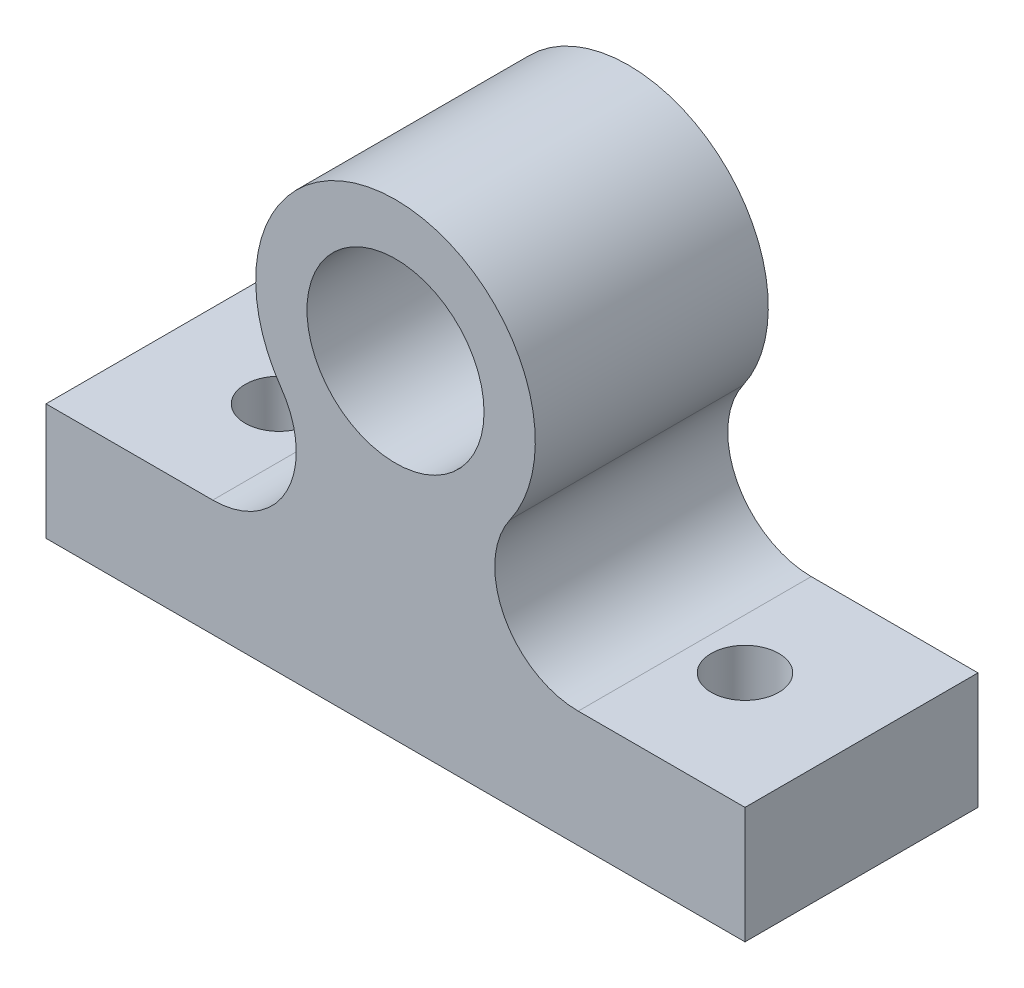
SolidWorks part; units mm, degrees
ref_plane "Front Plane" through (0, 0, 0) normal (0, 0, 1) x (1, 0, 0)
ref_plane "Top Plane" through (0, 0, 0) normal (0, 1, 0) x (1, 0, 0)
ref_plane "Right Plane" through (0, 0, 0) normal (1, 0, 0) x (0, 0, -1)
sketch "Sketch1" plane through (0, 0, 0) normal (0, 0, 1) x (1, 0, 0)
  line L0 (0, 0) -> (38.1, 0)
  line L1 (38.1, 0) -> (38.1, 6.35)
  line L2 (38.1, 6.35) -> (29.0108, 6.35)
  line L3 (0, 0) -> (0, 6.35)
  line L4 (0, 6.35) -> (9.0892, 6.35)
  line L5 (19.05, 17.8957) -> (19.05, 0) construction
  line L6 (19.05, 25.5157) -> (19.05, 0) construction
  arc A0 (9.0892, 6.35) -> (12.8139, 13.5168) centre (9.0892, 10.9013) ccw
  arc A1 (29.0108, 6.35) -> (25.2861, 13.5168) centre (29.0108, 10.9013) cw
  arc A2 (25.2861, 13.5168) -> (12.8139, 13.5168) centre (19.05, 17.8957) ccw
  circle A3 centre (19.05, 17.8957) radius 4.826
  point P13 (10.6884, 6.35)
  dimension "D4" = 15.24
  dimension "D5" = 9.652
  dimension "D6" = 25.5157
  dimension "D7" = 4.5513
  dimension "D1" = 38.1
  dimension "D2" = 6.35
  dimension "D3" = 6.35
extrude "Boss-Extrude1" add sketch "Sketch1" along normal blind 12.7
sketch "Sketch2" plane through (0, 6.35, 0) normal (0, 1, 0) x (1, 0, 0)
  line L0 (0, -6.35) -> (6.35, -6.35) construction
  line L1 (0, -12.7) -> (0, 0) construction
  line L2 (6.35, -6.35) -> (6.35, 0) construction
  line L3 (9.0892, 0) -> (0, 0) construction
  line L4 (6.35, -6.35) -> (31.75, -6.35) construction
  circle A0 centre (6.35, -6.35) radius 1.8415
  circle A1 centre (31.75, -6.35) radius 1.8415
  dimension "D3" = 3.683
  dimension "D1" = 25.4
  dimension "D2" = 6.35
extrude "Cut-Extrude1" cut sketch "Sketch2" against normal through all both and the other way through all
